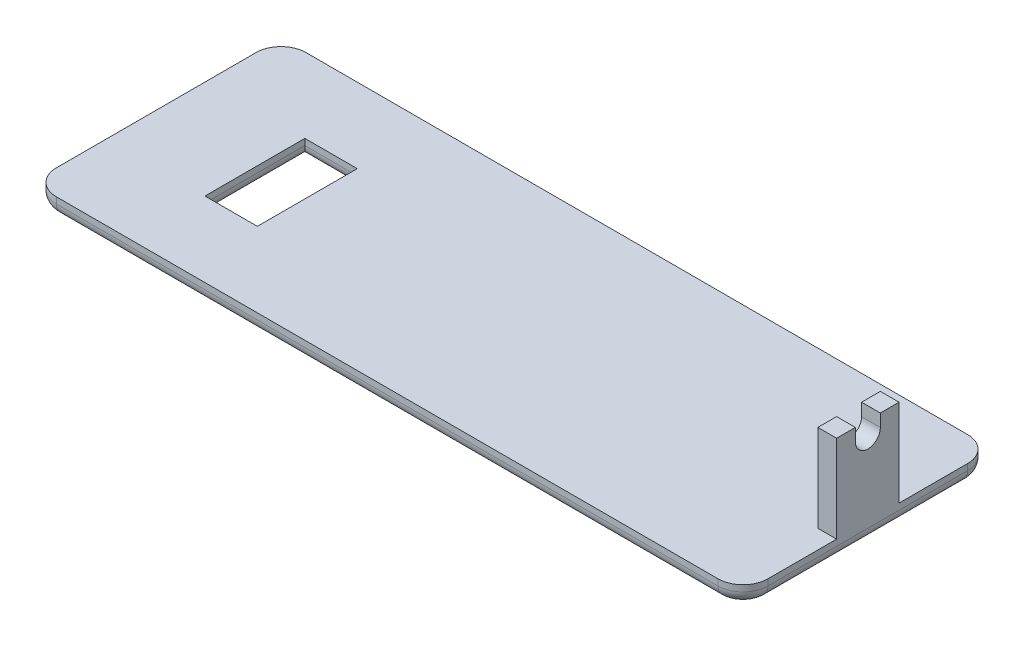
SolidWorks part; units mm, degrees
ref_plane "Front Plane" through (0, 0, 0) normal (0, 0, 1) x (1, 0, 0)
ref_plane "Top Plane" through (0, 0, 0) normal (0, 1, 0) x (1, 0, 0)
ref_plane "Right Plane" through (0, 0, 0) normal (1, 0, 0) x (0, 0, -1)
sketch "Sketch1" plane through (0, 0, 0) normal (0, 1, 0) x (1, 0, 0)
  line L1 (-72.39, -25.4) -> (72.39, -25.4)
  line L2 (-72.39, -25.4) -> (-72.39, 25.4)
  line L3 (-72.39, 25.4) -> (72.39, 25.4)
  line L4 (72.39, -25.4) -> (72.39, 25.4)
  line L5 (-72.39, -25.4) -> (72.39, 25.4) construction
  line L6 (-72.39, 25.4) -> (72.39, -25.4) construction
  point P0 (0, 0)
  dimension "D1" = 144.78
  dimension "D2" = 50.8
extrude "Boss-Extrude1" add sketch "Sketch1" along normal blind 3.81
sketch "Sketch2" plane through (0, 3.81, 0) normal (0, 1, 0) x (1, 0, 0)
  line L0 (72.39, -25.4) -> (72.39, 25.4) construction
  line L1 (72.39, 6.35) -> (68.58, 6.35)
  line L2 (72.39, 6.35) -> (72.39, -6.35)
  line L3 (72.39, -6.35) -> (68.58, -6.35)
  line L4 (68.58, 6.35) -> (68.58, -6.35)
  line L5 (72.39, 6.35) -> (68.58, 6.35) construction
extrude "Boss-Extrude2" add sketch "Sketch2" along normal blind 17.78
sketch "Sketch3" plane through (72.39, 0, 0) normal (1, 0, 0) x (0, 0, -1)
  line L0 (-2.54, 21.59) -> (2.54, 21.59)
  line L1 (-2.54, 21.59) -> (-2.54, 19.05)
  line L2 (2.54, 21.59) -> (2.54, 19.05)
  line L5 (-6.35, 21.59) -> (6.35, 21.59) construction
  arc A0 (2.54, 19.05) -> (-2.54, 19.05) centre (0, 19.05) cw
  point P5 (0, 21.59)
  dimension "D1" = 5.08
  dimension "D2" = 2.54
extrude "Cut-Extrude1" cut sketch "Sketch3" against normal up to next
sketch "Sketch4" plane through (0, 0, 0) normal (0, -1, 0) x (1, 0, 0)
  line L0 (-52.31, 25.4) -> (-52.31, -25.4) construction
  line L1 (-72.39, 25.4) -> (72.39, 25.4) construction
  line L2 (72.39, -25.4) -> (-72.39, -25.4) construction
  line L3 (-72.39, -25.4) -> (-72.39, 25.4) construction
  line L4 (-41.642, 25.4) -> (-41.642, -25.4) construction
  line L5 (-52.31, 0) -> (-41.642, 0) construction
  line L7 (-41.642, -10.16) -> (-52.31, -10.16)
  line L8 (-41.642, -10.16) -> (-41.642, 10.16)
  line L9 (-41.642, 10.16) -> (-52.31, 10.16)
  line L10 (-52.31, -10.16) -> (-52.31, 10.16)
  line L11 (-41.642, -10.16) -> (-52.31, 10.16) construction
  line L12 (-41.642, 10.16) -> (-52.31, -10.16) construction
  point P12 (-46.976, 0)
  dimension "D1" = 10.668
  dimension "D2" = 20.08
  dimension "D3" = 20.32
extrude "Cut-Extrude2" cut sketch "Sketch4" against normal through all
fillet "Fillet3" radius 5.08 4 edges at (-72.39, 1.905, -25.4) (-72.39, 1.905, 25.4) (72.39, 1.905, 25.4) (72.39, 1.905, -25.4)
fillet "Fillet4" radius 2.54 12 edges at (-72.39, 0, 0) (-70.9021, 0, 23.9121) (0, 0, 25.4) (70.9021, 0, 23.9121) (72.39, 0, 0) (70.9021, 0, -23.9121) (0, 0, -25.4) (-46.976, 0, 10.16) (-52.31, 0, 0) (-46.976, 0, -10.16) (-41.642, 0, 0) (-70.9021, 0, -23.9121)
